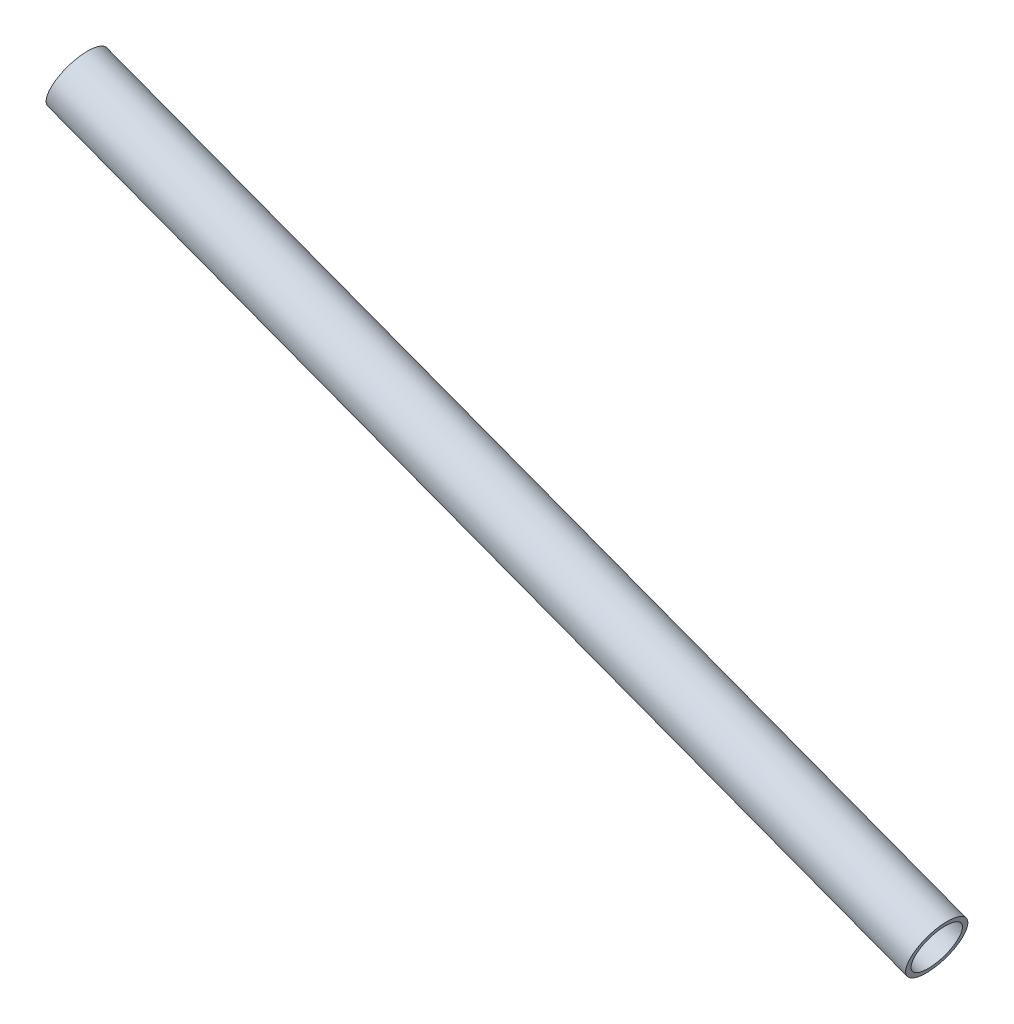
SolidWorks part; units mm, degrees
ref_plane "Front" through (0, 0, 0) normal (0, 0, 1) x (1, 0, 0)
ref_plane "Top" through (0, 0, 0) normal (0, 1, 0) x (1, 0, 0)
ref_plane "Right" through (0, 0, 0) normal (1, 0, 0) x (0, 0, -1)
sketch "Sketch1" plane through (0, 0, 0) normal (0, 0, 1) x (1, 0, 0)
  line L0 (-239.9095, -1718.7565) -> (-518.6483, -1613.6993)
  line L1 (-518.6483, -1613.6993) -> (-518.066, -1612.1544)
  line L2 (-518.066, -1612.1544) -> (-239.3273, -1717.2116)
  line L3 (-239.3273, -1717.2116) -> (-239.9095, -1718.7565)
  line L4 (-236.5502, -1709.8436) -> (-515.289, -1604.7864) construction
  line L5 (-190.5, -1727.2) -> (-571.5, -1583.6003) construction
  line L6 (-236.5502, -1709.8436) -> (-239.9095, -1718.7565) construction
  line L7 (-515.289, -1604.7864) -> (-518.6483, -1613.6993) construction
  dimension "D1" = 1.651
  dimension "D2" = 9.525
revolve "Revolve1" add sketch "Sketch1" angle 360 about L4
equation "\"D1@Sketch1\"=\"a arm tube thickness@FS2-SU-FS-A-0002-V1, FRONT LEFT SUSPENSION.SLDASM\""
equation "\"D2@Sketch1\"=\"a arm tube diameter@FS2-SU-FS-A-0002-V1, FRONT LEFT SUSPENSION.SLDASM\"/2"
